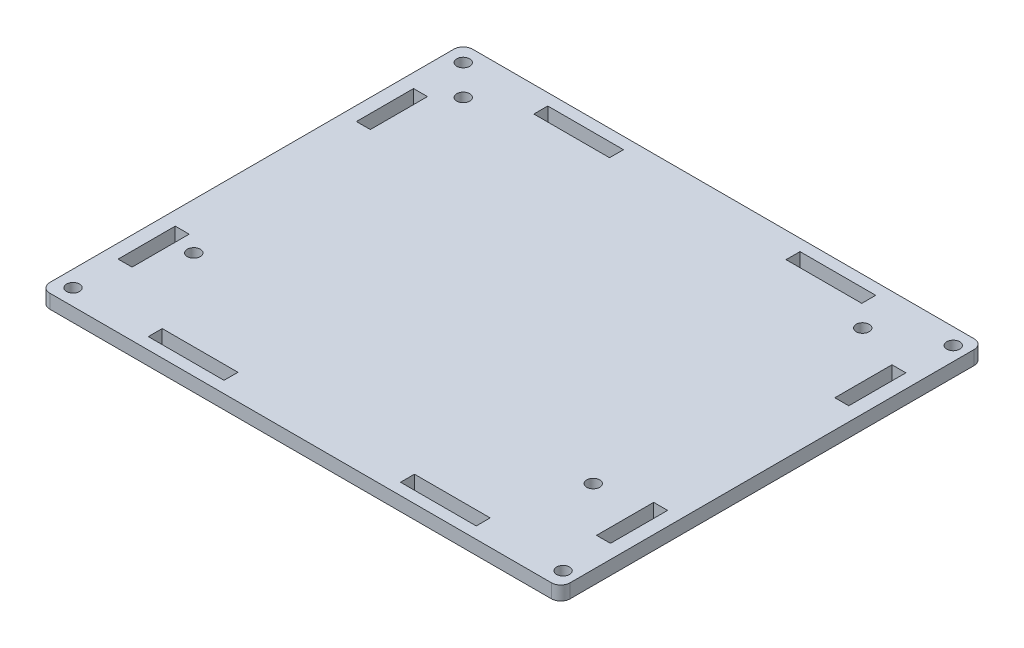
SolidWorks part; units mm, degrees
ref_plane "Alzado" through (0, 0, 0) normal (0, 0, 1) x (1, 0, 0)
ref_plane "Planta" through (0, 0, 0) normal (0, 1, 0) x (1, 0, 0)
ref_plane "Vista lateral" through (0, 0, 0) normal (1, 0, 0) x (0, 0, -1)
sketch "Croquis1" plane through (0, 0, 0) normal (0, 1, 0) x (1, 0, 0)
  line L1 (-54, 45.5) -> (54, 45.5)
  line L2 (-56, 43.5) -> (-56, -43.5)
  line L3 (-54, -45.5) -> (54, -45.5)
  line L4 (56, 43.5) -> (56, -43.5)
  line L5 (-56, 45.5) -> (56, -45.5) construction
  line L6 (-56, -45.5) -> (56, 45.5) construction
  line L7 (-35.3, 43) -> (-19, 43)
  line L8 (-35.3, 43) -> (-35.3, 40)
  line L9 (-35.3, 40) -> (-19, 40)
  line L10 (-19, 43) -> (-19, 40)
  line L11 (19, 43) -> (35.3, 43)
  line L12 (19, 43) -> (19, 40)
  line L13 (19, 40) -> (35.3, 40)
  line L14 (35.3, 43) -> (35.3, 40)
  line L15 (-35.3, -40) -> (-19, -40)
  line L16 (-35.3, -40) -> (-35.3, -43)
  line L17 (-35.3, -43) -> (-19, -43)
  line L18 (-19, -40) -> (-19, -43)
  line L19 (19, -40) -> (35.3, -40)
  line L20 (19, -40) -> (19, -43)
  line L21 (19, -43) -> (35.3, -43)
  line L22 (35.3, -40) -> (35.3, -43)
  line L23 (53, 31.8) -> (50, 31.8)
  line L24 (53, 31.8) -> (53, 19.5)
  line L25 (53, 19.5) -> (50, 19.5)
  line L26 (50, 31.8) -> (50, 19.5)
  line L27 (50, -19.5) -> (53, -19.5)
  line L28 (50, -19.5) -> (50, -31.8)
  line L29 (50, -31.8) -> (53, -31.8)
  line L30 (53, -19.5) -> (53, -31.8)
  line L31 (-50, 31.8) -> (-53, 31.8)
  line L32 (-50, 31.8) -> (-50, 19.5)
  line L33 (-50, 19.5) -> (-53, 19.5)
  line L34 (-53, 31.8) -> (-53, 19.5)
  line L35 (-50, -19.5) -> (-53, -19.5)
  line L36 (-50, -19.5) -> (-50, -31.8)
  line L37 (-50, -31.8) -> (-53, -31.8)
  line L38 (-53, -19.5) -> (-53, -31.8)
  arc A0 (56, 43.5) -> (54, 45.5) centre (54, 43.5) ccw
  arc A1 (56, -43.5) -> (54, -45.5) centre (54, -43.5) cw
  arc A2 (-54, -45.5) -> (-56, -43.5) centre (-54, -43.5) cw
  arc A3 (-56, 43.5) -> (-54, 45.5) centre (-54, 43.5) cw
  point P0 (0, 0)
  dimension "D7" = 2
  dimension "D1" = 91
  dimension "D2" = 112
  dimension "D3" = 3
  dimension "D4" = 3
  dimension "D5" = 3
  dimension "D6" = 3
  dimension "D8" = 16.3
  dimension "D9" = 16.3
  dimension "D10" = 12.3
  dimension "D11" = 12.3
  dimension "D12" = 20.7
  dimension "D13" = 20.7
  dimension "D14" = 2.5
  dimension "D15" = 2.5
  dimension "D16" = 3
  dimension "D17" = 3
  dimension "D18" = 13.7
  dimension "D19" = 13.7
  dimension "D20" = 80
  dimension "D21" = 100
extrude "Saliente-Extruir1" add sketch "Croquis1" along normal blind 3
sketch "Croquis2" plane through (0, 0, 0) normal (0, -1, 0) x (1, 0, 0)
  line L0 (56, 43.5) -> (56, -43.5) construction
  line L1 (54, -45.5) -> (-54, -45.5) construction
  circle A0 centre (53, -42) radius 1.4
  circle A4 centre (-52.5, -42) radius 1.4
  circle A5 centre (-52.5, 42) radius 1.4
  circle A6 centre (53, 42) radius 1.4
  dimension "D1" = 2.8
  dimension "D2" = 3
  dimension "D3" = 3.5
  dimension "D6" = 84
  dimension "D7" = 105.5
  dimension "D4" = 2
  dimension "D5" = 2
extrude "Cortar-Extruir1" cut sketch "Croquis2" against normal up to next
sketch "Croquis3" plane through (0, 0, 0) normal (0, 1, 0) x (1, 0, 0)
  line L2 (-54, -45.5) -> (54, -45.5) construction
  line L3 (56, -43.5) -> (56, 43.5) construction
  line L4 (54, 45.5) -> (-54, 45.5) construction
  line L5 (-56, 43.5) -> (-56, -43.5) construction
  circle A0 centre (40, -22.5) radius 1.4
  circle A1 centre (40, 35.5) radius 1.4
  circle A2 centre (-46, 35.5) radius 1.4
  circle A3 centre (-46, -22.5) radius 1.4
  dimension "D1" = 16
  dimension "D2" = 2.8
  dimension "D4" = 2.8
  dimension "D7" = 10
  dimension "D9" = 2.8
  dimension "D10" = 23
  dimension "D12" = 2.8
  dimension "D3" = 23
  dimension "D5" = 16
  dimension "D6" = 10
  dimension "D8" = 10
  dimension "D11" = 10
extrude "Cortar-Extruir2" cut sketch "Croquis3" along normal up to next
